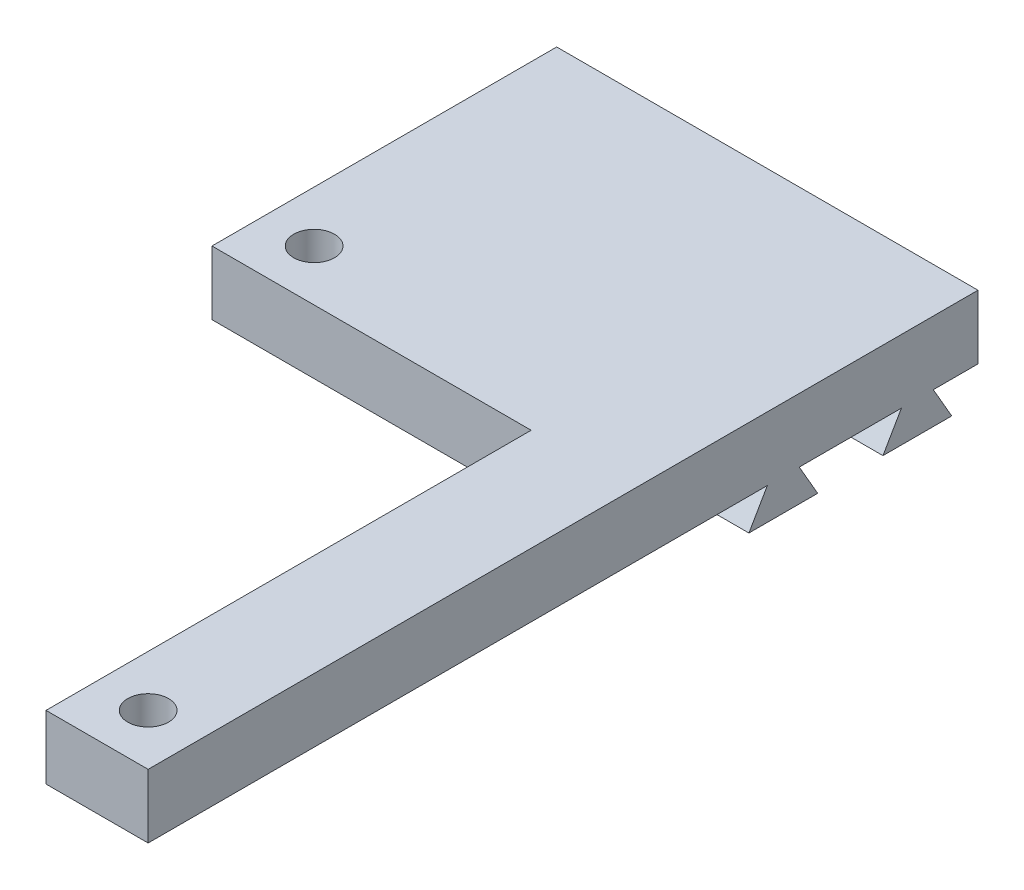
SolidWorks part; units mm, degrees
ref_plane "Front Plane" through (0, 0, 0) normal (0, 0, 1) x (1, 0, 0)
ref_plane "Top Plane" through (0, 0, 0) normal (0, 1, 0) x (1, 0, 0)
ref_plane "Right Plane" through (0, 0, 0) normal (1, 0, 0) x (0, 0, -1)
sketch "Sketch1" plane through (0, 0, 0) normal (0, 1, 0) x (1, 0, 0)
  line L0 (-16.5, 10) -> (8.5, 10)
  line L1 (8.5, -30) -> (16.5, -30)
  line L2 (-16.5, 10) -> (-16.5, 30)
  line L3 (-16.5, 30) -> (16.5, 30)
  line L4 (16.5, -30) -> (16.5, 30)
  line L7 (8.5, 10) -> (8.5, -30)
  point P0 (0, 0)
  dimension "D1" = 33
  dimension "D2" = 60
  dimension "D3" = 25
  dimension "D4" = 20
extrude "Boss-Extrude1" add sketch "Sketch1" along normal blind 5
sketch "Sketch3" plane through (-16.5, 0, 0) normal (-1, 0, 0) x (0, 0, 1)
  line L0 (-26.5, 0) -> (-27.9434, -2.5)
  line L1 (-30, 0) -> (-10, 0) construction
  line L2 (-27.9434, -2.5) -> (-22.5566, -2.5)
  line L3 (-22.5566, -2.5) -> (-24, 0)
  line L4 (-24, 0) -> (-26.5, 0)
  line L5 (-20, 9.1936) -> (-20, -9.1936)
  line L6 (-17.4434, -2.5) -> (-16, 0)
  line L7 (-12.0566, -2.5) -> (-17.4434, -2.5)
  line L8 (-13.5, 0) -> (-12.0566, -2.5)
  line L9 (-16, 0) -> (-13.5, 0)
  point P9 (-20, 0)
  line M6 (-30, 0) -> (-10, 0)
  dimension "D1" = 2.5
  dimension "D2" = 3.5
  dimension "D3" = 60
  dimension "D4" = 60
  dimension "D5" = 2.5
  dimension "D6" = 5.3868
extrude "Boss-Extrude3" add sketch "Sketch3" against normal blind 33 contours L2 L3 L0 M6 | L8 L6 L7 M6
sketch "Sketch4" plane through (0, 0, -10) normal (0, 0, 1) x (1, 0, 0)
  line L1 (-16.5, 5) -> (8.5, 5)
  line L2 (-16.5, 5) -> (-16.5, 0)
  line L3 (-16.5, 0) -> (8.5, 0)
  line L4 (8.5, 5) -> (8.5, 0)
extrude "Boss-Extrude4" add sketch "Sketch4" along normal blind 7
sketch "Sketch5" plane through (0, 0, 30) normal (0, 0, 1) x (1, 0, 0)
  line L1 (8.5, 5) -> (16.5, 5)
  line L2 (8.5, 5) -> (8.5, 0)
  line L3 (8.5, 0) -> (16.5, 0)
  line L4 (16.5, 5) -> (16.5, 0)
extrude "Boss-Extrude5" add sketch "Sketch5" along normal blind 5
sketch "Sketch6" plane through (0, 5, 0) normal (0, 1, 0) x (1, 0, 0)
  line L0 (-16.5, 30) -> (-16.5, 3) construction
  line L1 (8.5, 3) -> (-16.5, 3) construction
  line L2 (16.5, -35) -> (8.5, -35) construction
  line L3 (8.5, 3) -> (8.5, -35) construction
  circle A0 centre (-12.5, 7) radius 1.6
  circle A1 centre (12.5, -31) radius 1.6
  dimension "D3" = 3.2
  dimension "D4" = 3.2
  dimension "D1" = 4
  dimension "D2" = 4
  dimension "D5" = 4
  dimension "D6" = 4
extrude "Cut-Extrude1" cut sketch "Sketch6" against normal through all
